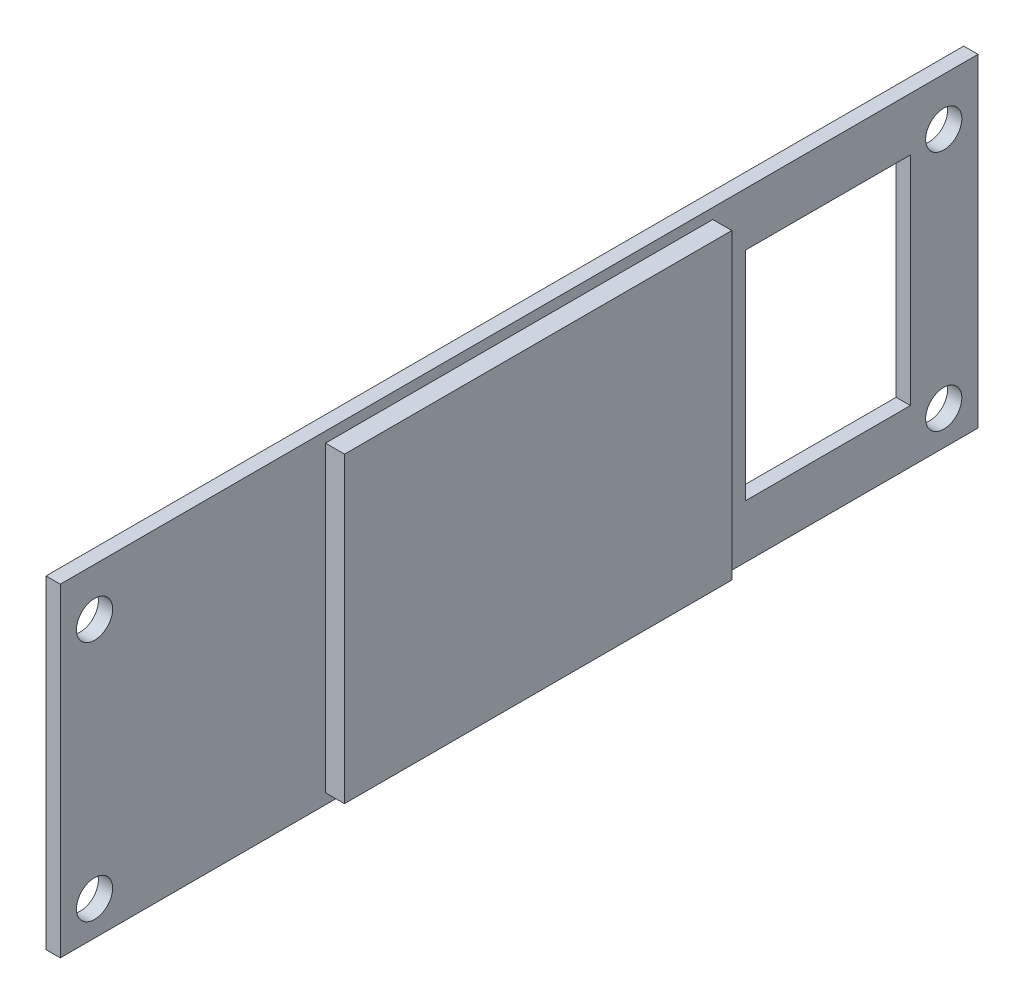
SolidWorks part; units mm, degrees
ref_plane "Front Plane" through (0, 0, 0) normal (0, 0, 1) x (1, 0, 0)
ref_plane "Top Plane" through (0, 0, 0) normal (0, 1, 0) x (1, 0, 0)
ref_plane "Right Plane" through (0, 0, 0) normal (1, 0, 0) x (0, 0, -1)
sketch "Sketch1" plane through (0, 0, 0) normal (1, 0, 0) x (0, 0, -1)
  line L1 (-61.214, -21.59) -> (61.214, -21.59)
  line L2 (-61.214, -21.59) -> (-61.214, 21.59)
  line L3 (-61.214, 21.59) -> (61.214, 21.59)
  line L4 (61.214, -21.59) -> (61.214, 21.59)
  line L5 (-61.214, -21.59) -> (61.214, 21.59) construction
  line L6 (-61.214, 21.59) -> (61.214, -21.59) construction
  point P0 (0, 0)
  dimension "D1" = 122.428
  dimension "D2" = 43.18
extrude "Boss-Extrude1" add sketch "Sketch1" against normal blind 1.905
sketch "Sketch2" plane through (0, 0, 0) normal (1, 0, 0) x (0, 0, -1)
  line L0 (-61.214, 21.59) -> (-61.214, -21.59) construction
  line L1 (61.214, 21.59) -> (-61.214, 21.59) construction
  line L2 (-61.214, -21.59) -> (61.214, -21.59) construction
  circle A0 centre (-56.642, 15.24) radius 2.413
  circle A1 centre (-56.642, -17.018) radius 2.413
  circle A2 centre (56.642, 15.24) radius 2.413
  circle A3 centre (56.642, -17.018) radius 2.413
  dimension "D1" = 4.826
  dimension "D3" = 6.35
  dimension "D4" = 4.826
  dimension "D5" = 4.572
  dimension "D2" = 4.572
extrude "Cut-Extrude1" cut sketch "Sketch2" against normal up to surface (1.905 mm away) up to face at (-1.905, 0, 0)
sketch "Sketch3" plane through (0, 0, 0) normal (1, 0, 0) x (0, 0, -1)
  arc A0 (-10.6362, -15.8042) -> (10.6362, -15.8042) centre (0, 0) ccw
  arc A2 (-15.8042, 10.6362) -> (-10.6362, 15.8042) centre (-15.7154, 15.7154) ccw
  arc A3 (15.8042, 10.6362) -> (10.6362, 15.8042) centre (15.7154, 15.7154) cw
  arc A4 (-15.8042, -10.6362) -> (-10.6362, -15.8042) centre (-15.7154, -15.7154) cw
  arc A5 (15.8042, -10.6362) -> (10.6362, -15.8042) centre (15.7154, -15.7154) ccw
  arc A6 (15.8042, -10.6362) -> (15.8042, 10.6362) centre (0, 0) ccw
  arc A7 (10.6362, 15.8042) -> (-10.6362, 15.8042) centre (0, 0) ccw
  arc A8 (-15.8042, 10.6362) -> (-15.8042, -10.6362) centre (0, 0) ccw
extrude "Cut-Extrude2" cut sketch "Sketch3" against normal up to surface (1.905 mm away) up to face at (-1.905, -17.018, -54.229)
sketch "Sketch4" plane through (-1.905, 0, 0) normal (-1, 0, 0) x (0, 0, 1)
  line L1 (-52.197, 14.478) -> (-30.226, 14.478)
  line L2 (-52.197, 14.478) -> (-52.197, -14.478)
  line L3 (-52.197, -14.478) -> (-30.226, -14.478)
  line L4 (-30.226, 14.478) -> (-30.226, -14.478)
extrude "Cut-Extrude3" cut sketch "Sketch4" against normal up to surface (1.905 mm away) up to face at (0, 0, 0)
sketch "Sketch5" plane through (0, 0, 0) normal (1, 0, 0) x (0, 0, -1)
  line L1 (-25.8339, -20.1934) -> (25.8339, -20.1934)
  line L2 (-25.8339, -20.1934) -> (-25.8339, 20.1934)
  line L3 (-25.8339, 20.1934) -> (25.8339, 20.1934)
  line L4 (25.8339, -20.1934) -> (25.8339, 20.1934)
  line L5 (-25.8339, -20.1934) -> (25.8339, 20.1934) construction
  line L6 (-25.8339, 20.1934) -> (25.8339, -20.1934) construction
  point P0 (0, 0)
extrude "Boss-Extrude2" add sketch "Sketch5" along normal blind 2.54
